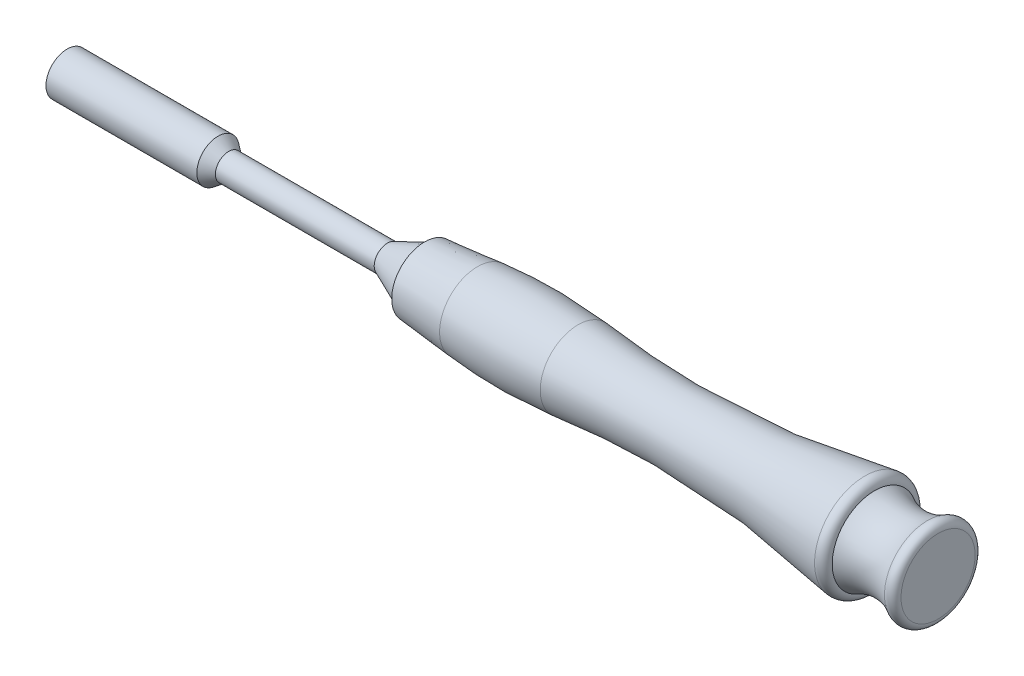
SolidWorks part; units mm, degrees
ref_plane "Front Plane" through (0, 0, 0) normal (0, 0, 1) x (1, 0, 0)
ref_plane "Top Plane" through (0, 0, 0) normal (0, 1, 0) x (1, 0, 0)
ref_plane "Right Plane" through (0, 0, 0) normal (1, 0, 0) x (0, 0, -1)
ref_axis "Axis1" through (184.722, 0, 0) along (-1, 0, 0)
sketch "Sketch1" plane through (0, 0, 0) normal (0, 0, 1) x (1, 0, 0)
  line L0 (0, 4) -> (28.5, 4)
  line L1 (28.5, 4) -> (30.5, 2.5)
  line L2 (30.5, 2.5) -> (60.5, 2.5)
  line L3 (60.5, 2.5) -> (60.5, 0)
  line L5 (0, 0) -> (60.5, 0)
  line L7 (0, 4) -> (0, 0)
  dimension "D2" = 4
  dimension "D3" = 2.5
  dimension "D4" = 28.5
  dimension "D5" = 30.5
  dimension "D8" = 60.5
revolve "AluminiumPart" add sketch "Sketch1" angle 360 about axis through (184.722, 0, 0) along (-1, 0, 0)
sketch "Sketch2" plane through (0, 0, 0) normal (-1, 0, 0) x (0, 0, 1)
  line L0 (-2.8, 1.6166) -> (0, 3.2332)
  line L1 (0, 3.2332) -> (2.8, 1.6166)
  line L2 (2.8, 1.6166) -> (2.8, -1.6166)
  line L3 (2.8, -1.6166) -> (0, -3.2332)
  line L4 (0, -3.2332) -> (-2.8, -1.6166)
  line L5 (-2.8, -1.6166) -> (-2.8, 1.6166)
  circle A0 centre (0, 0) radius 3.2332 construction
  point P9 (-1.7236, 1.0586)
  point P10 (-0.1874, 2.014)
  point P11 (1.7236, 1.0586)
  point P12 (1.8364, -0.848)
  point P13 (0, -2.0227)
  point P14 (-1.8696, -0.772)
  dimension "D1" = 5.6
extrude "HexagonalHead" cut sketch "Sketch2" against normal blind 5.25
sketch "Sketch3" plane through (0, 0, 0) normal (-1, 0, 0) x (0, 0, 1)
  circle A0 centre (0, 0) radius 2.5
  dimension "D1" = 5
extrude "CircularCentralHole" cut sketch "Sketch3" against normal blind 24
sketch "Sketch4" plane through (0, 0, 0) normal (0, 0, 1) x (1, 0, 0)
  line L0 (60.5, 0) -> (60.5, 2.5)
  line L1 (119.24, 0) -> (-58.74, 0) construction
  line L2 (60.5, 2.5) -> (67.5, 5.5)
  line L3 (67.5, 5.5) -> (67.5, 0)
  line L4 (67.5, 0) -> (60.5, 0)
  line L5 (60.5, -2.5) -> (60.5, 2.5) construction
  point P4 (60.5, 2.5)
  point P9 (69.5285, 0)
  point P10 (67.5, 5.5)
  point P11 (60.5, 1.9247)
  point P13 (67.5, 0)
  dimension "D1" = 7
  dimension "D2" = 5.5
revolve "FirstGreenPart" add sketch "Sketch4" angle 360 about axis through (184.722, 0, 0) along (-1, 0, 0)
sketch "Sketch5" plane through (0, 0, 0) normal (0, 0, 1) x (1, 0, 0)
  line L0 (67.5, 6.1957) -> (77.5, 7.15)
  line L1 (67.5, -5.5) -> (67.5, 5.5) construction
  line L2 (96.5, 7.15) -> (96.5, 0)
  line L3 (119.24, 0) -> (-58.74, 0) construction
  line L4 (96.5, 0) -> (67.5, 0)
  line L5 (67.5, 0) -> (67.5, 6.1957)
  arc A0 (96.5, 7.15) -> (77.5, 7.15) centre (87, -92.3977) ccw
  point P7 (0, 0)
  point P11 (67.5, 5.495)
  point P12 (77.5, 7.15)
  point P13 (87, 7.6023)
  dimension "D2" = 7.15
  dimension "D1" = 29
  dimension "D3" = 10
  dimension "D4" = 100
revolve "FirstBlackPart" add sketch "Sketch5" angle 360 about axis through (184.722, 0, 0) along (-1, 0, 0)
sketch "Sketch6" plane through (0, 0, 0) normal (0, 0, 1) x (1, 0, 0)
  line L0 (152.5, 8) -> (152.5, 0)
  line L1 (152.5, 0) -> (96.5, 0)
  line L2 (119.24, 0) -> (-58.74, 0) construction
  line L3 (96.5, 0) -> (96.5, 7.15)
  line L4 (96.5, -7.15) -> (96.5, 7.15) construction
  arc A0 (150.6699, 9.5) -> (96.5, 7.15) centre (116.029, 182.4976) cw
  arc A1 (150.6699, 9.5) -> (152.5, 8) centre (150.9702, 8) cw
  arc A4 (96.5, 7.15) -> (77.5, 7.15) centre (87, -92.3977) ccw construction
  point P1 (119.5, 6.1)
  point P15 (96.5, 7.15)
  dimension "D5" = 23
  dimension "D1" = 56
  dimension "D2" = 8
  dimension "D3" = 9.5
  dimension "D4" = 6.1
revolve "SecondGreenPart" add sketch "Sketch6" angle 360 about axis through (184.722, 0, 0) along (-1, 0, 0)
sketch "Sketch7" plane through (0, 0, 0) normal (0, 0, 1) x (1, 0, 0)
  line L0 (152.5, 0) -> (152.5, 8)
  line L1 (152.5, 0) -> (164.5, 0)
  line L2 (164.5, 0) -> (164.5, 7)
  line L3 (184.722, 0) -> (-61.3483, 0) construction
  arc A0 (162.5, 8.1267) -> (152.5, 8) centre (157.3924, 16.5561) cw
  arc A1 (162.5, 8.1267) -> (164.5, 7) centre (163.1827, 7) cw
  point P5 (0, 0)
  point P17 (157.3924, 6.7)
  dimension "D1" = 12
  dimension "D2" = 7
  dimension "D3" = 2
  dimension "D4" = 6.7
revolve "LastBlackPart" add sketch "Sketch7" angle 360 about axis through (184.722, 0, 0) along (-1, 0, 0)
